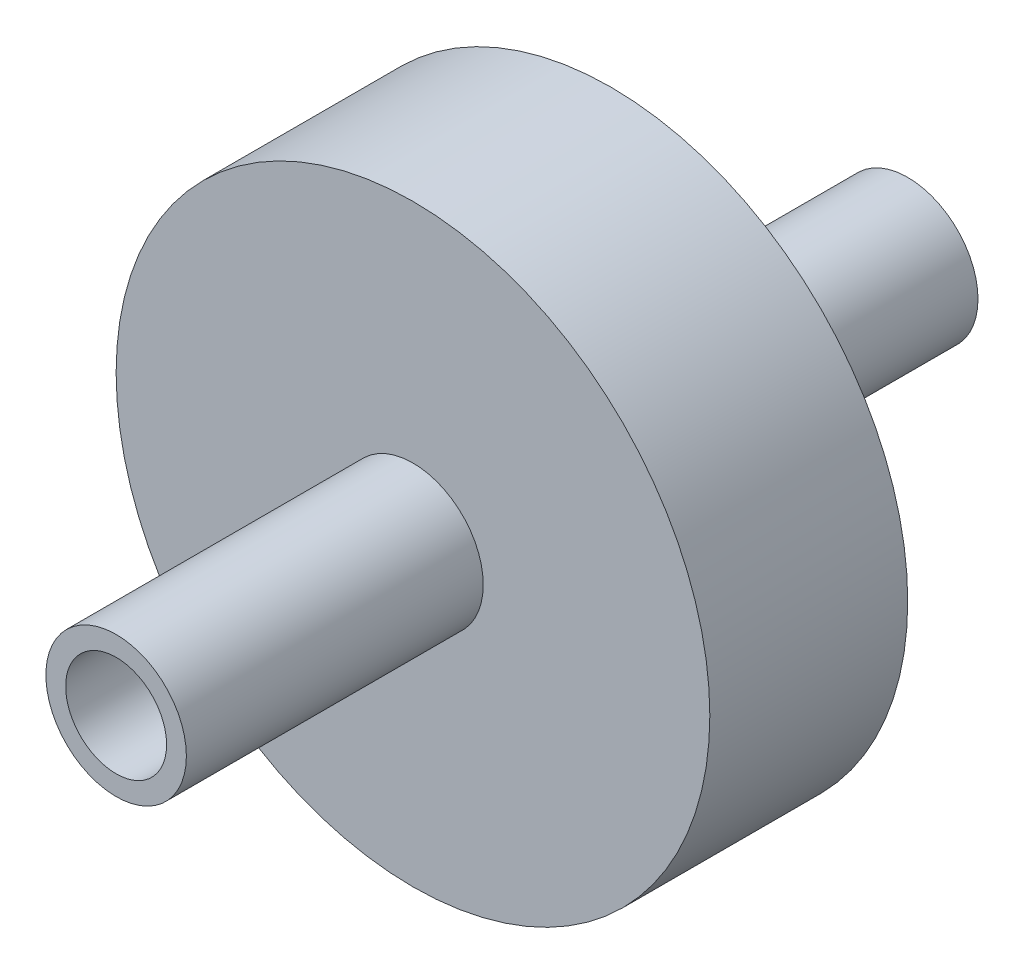
SolidWorks part; units mm, degrees
ref_plane "Front Plane" through (0, 0, 0) normal (0, 0, 1) x (1, 0, 0)
ref_plane "Top Plane" through (0, 0, 0) normal (0, 1, 0) x (1, 0, 0)
ref_plane "Right Plane" through (0, 0, 0) normal (1, 0, 0) x (0, 0, -1)
sketch "Sketch3" plane through (0, 0, 0) normal (0, 0, 1) x (1, 0, 0)
  circle A0 centre (0, 0) radius 15
  dimension "D1" = 30
extrude "Boss-Extrude1" add sketch "Sketch3" along normal blind 10
sketch "Sketch4" plane through (0, 0, 10) normal (0, 0, 1) x (1, 0, 0)
  circle A0 centre (0, 0) radius 2.55
  circle A1 centre (0, 0) radius 3.55
  dimension "D1" = 5.1
  dimension "D2" = 1
extrude "Boss-Extrude2" add sketch "Sketch4" along normal blind 15 and the other way blind 25
sketch "Sketch9" plane through (0, 0, 10) normal (0, 0, 1) x (1, 0, 0)
  circle A0 centre (0, 0) radius 2.55
extrude "Cut-Extrude1" cut sketch "Sketch9" against normal through all
